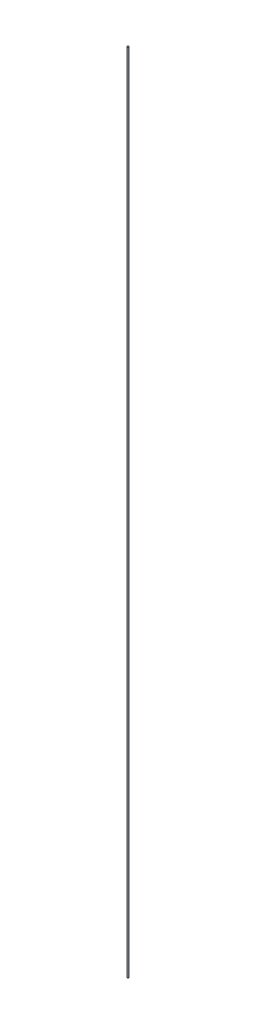
SolidWorks part; units mm, degrees
material "Hexcel AS4C (3000 Filaments)"
ref_plane "Front Plane" through (0, 0, 0) normal (0, 0, 1) x (1, 0, 0)
ref_plane "Top Plane" through (0, 0, 0) normal (0, 1, 0) x (1, 0, 0)
ref_plane "Right Plane" through (0, 0, 0) normal (1, 0, 0) x (0, 0, -1)
sketch "Sketch2" plane through (0, 0, 0) normal (0, 1, 0) x (1, 0, 0)
  circle A0 centre (0, 0) radius 1.27
  dimension "D1" = 2.54
extrude "Boss-Extrude3" add sketch "Sketch2" along normal blind 1282.7
